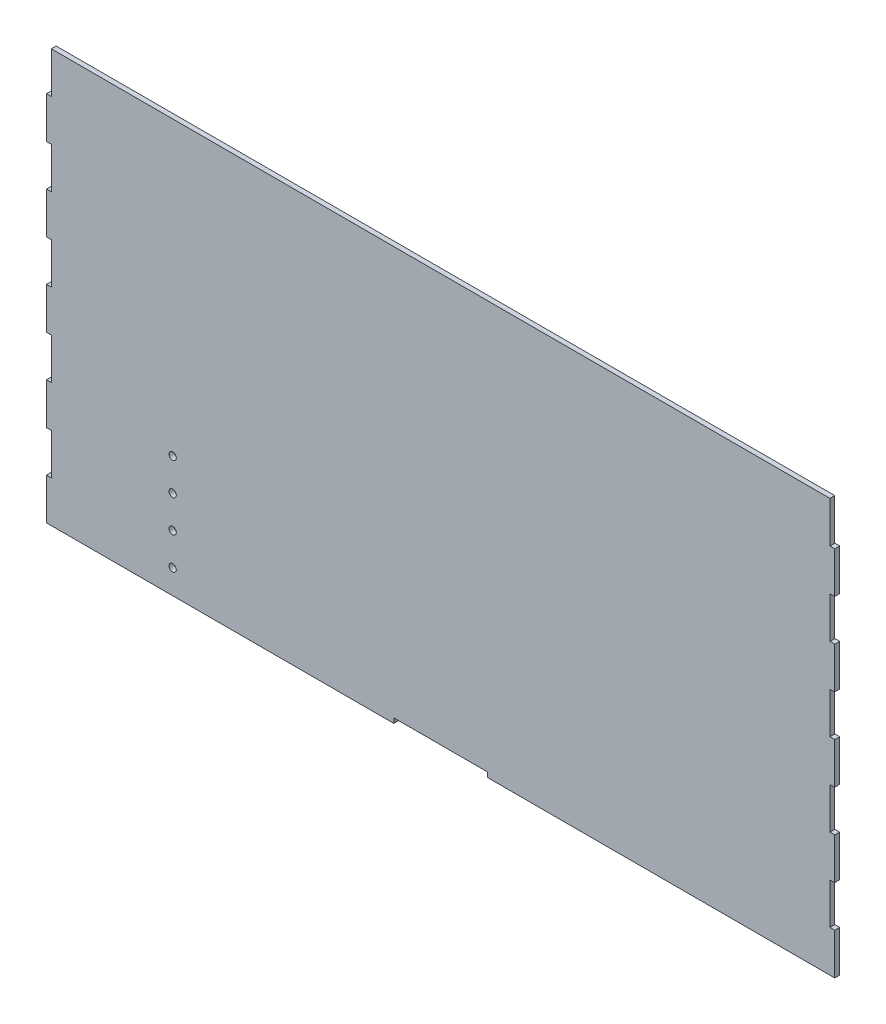
SolidWorks part; units mm, degrees
material "Pine"
ref_plane "Front Plane" through (0, 0, 0) normal (0, 0, 1) x (1, 0, 0)
ref_plane "Top Plane" through (0, 0, 0) normal (0, 1, 0) x (1, 0, 0)
ref_plane "Right Plane" through (0, 0, 0) normal (1, 0, 0) x (0, 0, -1)
sketch "Sketch1" plane through (0, 0, 0) normal (0, 0, 1) x (1, 0, 0)
  line L1 (-488.6875, 256) -> (488.6875, 256)
  line L2 (-488.6875, 256) -> (-488.6875, -256)
  line L3 (-488.6875, -256) -> (488.6875, -256)
  line L4 (488.6875, 256) -> (488.6875, -256)
  line L5 (-488.6875, 256) -> (488.6875, -256) construction
  line L6 (-488.6875, -256) -> (488.6875, 256) construction
  point P4 (0, 0)
  dimension "D1" = 977.375
  dimension "D2" = 512
  dimension "D3" = 0
  dimension "D4" = 0
extrude "Boss-Extrude1" add sketch "Sketch1" along normal blind 6
sketch "Sketch7" plane through (0, 0, 6) normal (0, 0, 1) x (1, 0, 0)
  line L0 (488.6875, -256) -> (488.6875, 256) construction
  line L1 (488.6875, -204.8) -> (482.6875, -204.8)
  line L2 (488.6875, -204.8) -> (488.6875, -153.6)
  line L3 (488.6875, -153.6) -> (482.6875, -153.6)
  line L4 (482.6875, -204.8) -> (482.6875, -153.6)
  line L5 (-488.6875, -256) -> (488.6875, -256) construction
  ellipse E0 centre (485.6875, -204.8) end of major axis (488.6875, -204.8) minor radius 0.2
  ellipse E1 centre (485.6875, -153.6) end of major axis (488.6875, -153.6) minor radius 0.2
  line M8 (488.6875, -256) -> (488.6875, 256)
  dimension "D1" = 6
  dimension "D2" = 51.2
  dimension "D3" = 51.2
  dimension "D4" = 0.2
  dimension "D5" = 0.2
extrude "Cut-Extrude3" cut sketch "Sketch7" against normal blind 10 contours E0 L3 L4 M8
pattern_linear "LPattern1" count 5 spacing 102.4 along (0, 1, 0) of "Cut-Extrude3"
sketch "Sketch8" plane through (0, 0, 6) normal (0, 0, 1) x (1, 0, 0)
  line L1 (482.6875, 256) -> (488.6875, 256)
  line L2 (482.6875, 256) -> (482.6875, 255.4193)
  line L3 (482.6875, 255.4193) -> (488.6875, 255.4193)
  line L4 (488.6875, 256) -> (488.6875, 255.4193)
  dimension "D1" = 6
  dimension "D2" = 0.5807
extrude "Cut-Extrude4" cut sketch "Sketch8" against normal blind 10
sketch "Sketch10" plane through (0, 0, 6) normal (0, 0, 1) x (1, 0, 0)
  line L0 (-488.6875, 256) -> (-488.6875, -256) construction
  line L1 (-488.6875, -204.8) -> (-482.6875, -204.8)
  line L2 (-488.6875, -204.8) -> (-488.6875, -153.6)
  line L3 (-488.6875, -153.6) -> (-482.6875, -153.6)
  line L4 (-482.6875, -204.8) -> (-482.6875, -153.6)
  line L5 (-488.6875, -256) -> (488.6875, -256) construction
  ellipse E0 centre (-485.6875, -204.8) end of major axis (-482.6875, -204.8) minor radius 0.2
  ellipse E1 centre (-485.6875, -153.6) end of major axis (-482.6875, -153.6) minor radius 0.2
  line M18 (-488.6875, 256) -> (-488.6875, -256)
  dimension "D1" = 6
  dimension "D2" = 102.4
  dimension "D3" = 51.2
  dimension "D4" = 0.2
  dimension "D5" = 0.2
extrude "Cut-Extrude5" cut sketch "Sketch10" against normal blind 10 contours E1 E0 L4 M18
pattern_linear "LPattern4" count 5 spacing 102.4 along (0, -1, 0) of "Cut-Extrude5"
sketch "Sketch11" plane through (0, 0, 6) normal (0, 0, 1) x (1, 0, 0)
  line L1 (-482.6875, 256) -> (-488.6875, 256)
  line L2 (-482.6875, 256) -> (-482.6875, 255.2668)
  line L3 (-482.6875, 255.2668) -> (-488.6875, 255.2668)
  line L4 (-488.6875, 256) -> (-488.6875, 255.2668)
  dimension "D1" = 6
  dimension "D2" = 0.7332
extrude "Cut-Extrude6" cut sketch "Sketch11" against normal blind 10 contours L3 L4 L1 L2
sketch "Sketch12" plane through (0, 0, 6) normal (0, 0, 1) x (1, 0, 0)
  line L0 (282.1875, 256) -> (282.1875, -256)
  line L1 (482.6875, 256) -> (-482.6875, 256) construction
  line L2 (-488.6875, -256) -> (488.6875, -256) construction
  line L3 (488.6875, 153.6) -> (488.6875, 204.8) construction
  line L4 (-282.1875, 256) -> (-282.1875, -256)
  line L5 (-488.6875, 204.8) -> (-488.6875, 153.6) construction
  line L6 (-206, 256) -> (-206, -256)
  dimension "D1" = 206.5
  dimension "D2" = 206.5
  dimension "D3" = 206
sketch "Sketch13" plane through (0, 0, 6) normal (0, 0, 1) x (1, 0, 0)
  line L0 (206, 256) -> (206, -256)
  line L1 (482.6875, 256) -> (-482.6875, 256) construction
  line L2 (-488.6875, -256) -> (488.6875, -256) construction
  dimension "D1" = 206
sketch "Sketch14" plane through (0, 0, 6) normal (0, 0, 1) x (1, 0, 0)
  line L1 (-58, -250.0304) -> (58, -250.0304)
  line L2 (-58, -250.0304) -> (-58, -256.0304)
  line L3 (-58, -256.0304) -> (58, -256.0304)
  line L4 (58, -250.0304) -> (58, -256.0304)
  line L5 (-58, -250.0304) -> (58, -256.0304) construction
  line L6 (-58, -256.0304) -> (58, -250.0304) construction
  point P4 (0, -253.0304)
  dimension "D1" = 148
  dimension "D2" = 148
extrude "Cut-Extrude9" cut sketch "Sketch14" against normal blind 10 contours L2 L1 L4 L3
sketch "Sketch15" plane through (0, 0, 6) normal (0, 0, 1) x (1, 0, 0)
  line L0 (-488.6875, -256) -> (-58, -256) construction
  line L1 (-282.1875, 256) -> (-282.1875, -256) construction
  circle A0 centre (-332.1875, -226) radius 4.5
  dimension "D1" = 30
  dimension "D3" = 9
  dimension "D2" = 50
extrude "Cut-Extrude11" cut sketch "Sketch15" against normal blind 10
pattern_linear "LPattern5" count 4 spacing 40 along (0, 1, 0) of "Cut-Extrude11"
